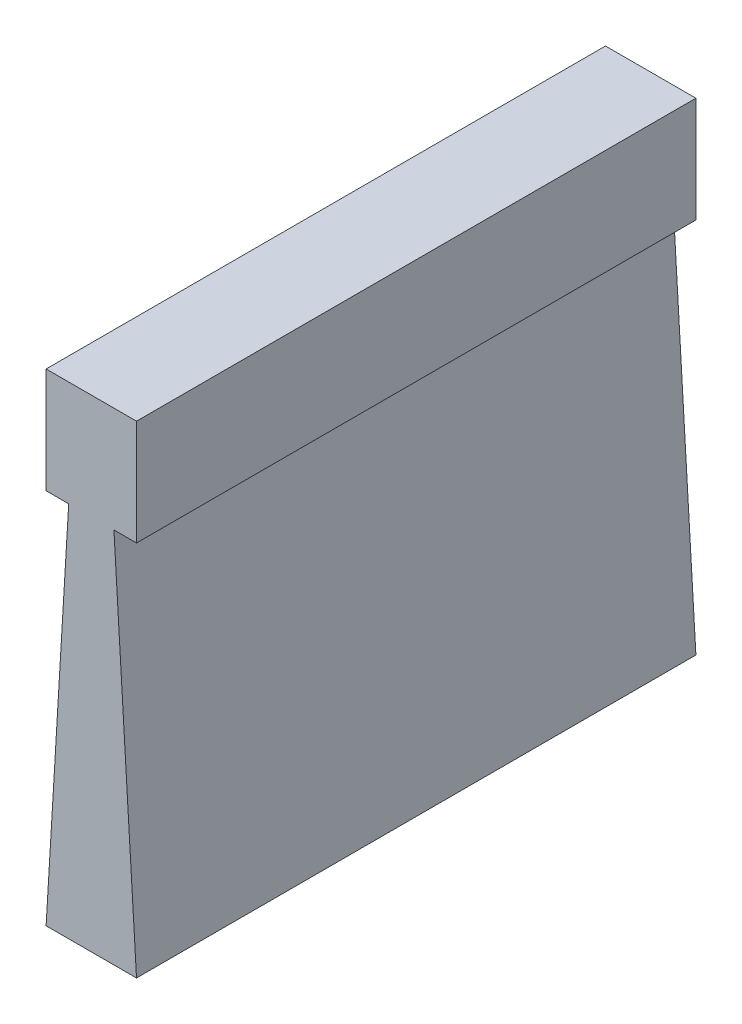
SolidWorks part; units mm, degrees
ref_plane "Front" through (0, 0, 0) normal (0, 0, 1) x (1, 0, 0)
ref_plane "Top" through (0, 0, 0) normal (0, 1, 0) x (1, 0, 0)
ref_plane "Right" through (0, 0, 0) normal (1, 0, 0) x (0, 0, -1)
sketch "Sketch1" plane through (0, 0, 0) normal (0, 0, 1) x (1, 0, 0)
  line L0 (-1.1906, 0) -> (1.1906, 0) construction
  line L1 (-1.1906, 0) -> (-2.3813, 0)
  line L2 (-2.3813, 0) -> (-2.3813, 5.5563)
  line L3 (-2.3813, 5.5563) -> (2.3813, 5.5563)
  line L4 (2.3813, 5.5563) -> (2.3813, 0)
  line L5 (1.1906, 0) -> (2.3813, 0)
  line L6 (-1.1906, 0) -> (-2.3812, -19.8437)
  line L7 (-2.3813, 0) -> (-2.3812, -19.8437) construction
  line L8 (-2.3812, -19.8437) -> (2.3813, -19.8437)
  line L9 (0, 0) -> (0, -19.8437) construction
  line L10 (1.1906, 0) -> (2.3813, -19.8437)
  dimension "D3" = 1.1906
extrude "Boss-Extrude1" add sketch "Sketch1" along normal mid plane 29.464
equation "\"D3@Sketch1\" = \"Width@Sketch1\"*.25"
